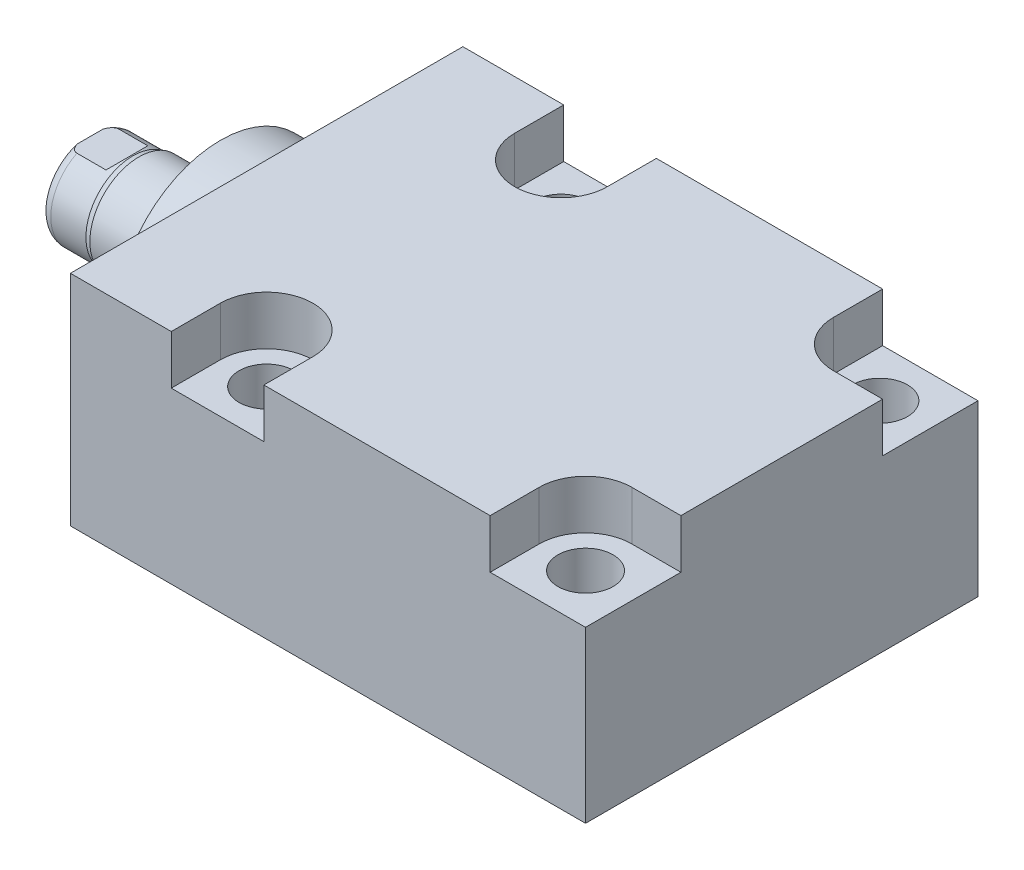
SolidWorks part; units mm, degrees
material "Alloy Steel"
ref_plane "Front Plane" through (0, 0, 0) normal (0, 0, 1) x (1, 0, 0)
ref_plane "Top Plane" through (0, 0, 0) normal (0, 1, 0) x (1, 0, 0)
ref_plane "Right Plane" through (0, 0, 0) normal (1, 0, 0) x (0, 0, -1)
ref_plane "Plane1" through (0, 0, 0) normal (1, 0, 0) x (0, 0, -1)
sketch "Sketch1" plane through (0, 0, 0) normal (1, 0, 0) x (0, 0, -1)
  line L0 (-25.4, 14.271) -> (25.4, 14.271)
  line L1 (25.4, 14.271) -> (25.4, -14.05)
  line L2 (25.4, -14.05) -> (-25.4, -14.05)
  line L3 (-25.4, -14.05) -> (-25.4, 14.271)
  line L4 (0, -24.4475) -> (0, 24.4475) construction
  dimension "D1" = 28.321
  dimension "D2" = 14.05
  dimension "D3" = 50.8
  dimension "D4" = 25.4
extrude "Extrude1" add sketch "Sketch1" along normal blind 66.675
sketch "Sketch5" plane through (0, 0, 0) normal (-1, 0, 0) x (0, 0, 1)
  circle A0 centre (0, 0) radius 13.5001
  dimension "D1" = 27.0002
extrude "Extrude2" add sketch "Sketch5" along normal blind 5.969
ref_plane "Plane5" through (0, 0, 0) normal (0, -1, 0) x (0, 0, 1)
sketch "Sketch6" plane through (0, 0, 0) normal (0, -1, 0) x (0, 0, 1)
  line L0 (0, 5.969) -> (-6.35, 5.969)
  line L1 (-6.35, 5.969) -> (-6.35, 22.86)
  line L2 (-6.35, 22.86) -> (0, 22.86)
  line L3 (0, 22.86) -> (0, 5.969)
  line L4 (0, -5.7546) -> (0, 21.1709) construction
  line L5 (13.5001, 5.969) -> (-13.5001, 5.969) construction
  line L6 (25.4, -66.675) -> (-25.4, -66.675) construction
  dimension "D1" = 89.535
  dimension "D2" = 12.7
revolve "Revolve1" add sketch "Sketch6" angle 360 about L4
ref_plane "Plane6" through (-18.5113, 3.2639, 0) normal (0, 0, 1) x (0, 1, 0)
sketch "S2D0001" plane through (-18.5113, 3.2639, 0) normal (0, 0, 1) x (0, 1, 0)
  line L0 (-0.7112, 2.7869) -> (-0.7112, -11.6533)
  line L1 (-3.2639, -13.1871) -> (-0.7112, -11.6533)
  line L2 (0.1905, 4.3487) -> (-3.2639, 4.3487)
  line L3 (-3.2639, 4.3487) -> (-3.2639, -13.1871)
  line L4 (-0.7112, 2.7869) -> (0.1905, 4.3487)
  line L5 (-3.2639, -18.5113) -> (-3.2639, 2.765) construction
  line L6 (3.0861, 4.3487) -> (-9.6139, 4.3487) construction
  dimension "D1" = 30
  dimension "D2" = 6.9088
  dimension "D3" = 5.1054
  dimension "D4" = 16.002
  dimension "D5" = 59
revolve "Cut-Revolve4" cut sketch "S2D0001" angle 360 about L5
ref_plane "Plane7" through (0, 0, 0) normal (0, 1, 0) x (0, 0, -1)
sketch "Sketch8" plane through (0, 0, 0) normal (0, 1, 0) x (0, 0, -1)
  line L0 (-6.35, 16.5354) -> (-6.096, 17.2974)
  line L1 (-6.096, 17.2974) -> (-6.096, 21.844)
  line L2 (0, 12.6594) -> (0, 20.8178) construction
  line L3 (-6.35, 16.5354) -> (-6.35, 22.86)
  line L4 (-5.7079, 22.86) -> (-6.35, 22.86)
  line L5 (6.35, 22.86) -> (-6.35, 22.86) construction
  line L6 (-6.35, 22.86) -> (-6.35, 5.969) construction
  arc A0 (-5.7079, 22.86) -> (-6.096, 21.844) centre (-4.572, 21.844) ccw
  dimension "D2" = 1.524
  dimension "D1" = 12.192
  dimension "D3" = 1.016
  dimension "D4" = 0.762
  dimension "D5" = 5.5626
revolve "Cut-Revolve5" cut sketch "Sketch8" angle 360 about L2
ref_plane "Plane11" through (0, 0, 0) normal (0, 0, -1) x (0, -1, 0)
sketch "Sketch12" plane through (0, 0, 0) normal (0, 0, -1) x (0, -1, 0)
  line L0 (5.461, 22.86) -> (5.461, 18.0848)
  line L1 (5.461, 18.0848) -> (6.096, 17.4498)
  line L2 (-5.461, 22.86) -> (-5.461, 18.0848)
  line L3 (-5.461, 18.0848) -> (-6.096, 17.4498)
  line L4 (5.461, 22.86) -> (6.096, 22.86)
  line L5 (0, 13.7262) -> (0, 20.767) construction
  line L6 (-6.096, 17.4498) -> (-6.096, 22.86)
  line L8 (6.096, 17.2974) -> (6.096, 21.844) construction
  line L9 (6.096, 17.4498) -> (6.096, 22.86)
  line L10 (-5.461, 22.86) -> (-6.096, 22.86)
  line L12 (5.7079, 22.86) -> (-5.7079, 22.86) construction
  dimension "D1" = 10.922
  dimension "D2" = 4.7752
  dimension "D3" = 45
extrude "Cut-Extrude4" cut sketch "Sketch12" against normal mid plane 60.96
hole_wizard "Hole2" positions "Sketch17" profile "Sketch16" legacy
sketch "Sketch17" plane through (0, 14.271, 0) normal (0, 1, 0) x (-1, 0, 0)
  line L0 (0, 0) -> (-59.3363, 0) construction
  line L1 (0, -25.4) -> (0, 25.4) construction
  point P0 (-19.05, -19.05)
  point P9 (-19.05, 19.05)
  dimension "D1" = 38.1
  dimension "D2" = 19.05
sketch "Sketch16" plane through (19.05, 14.271, -19.05) normal (1, 0, 0) x (0, 0, 1)
  line L0 (0, 0) -> (0, 28.321)
  line L1 (0, 28.321) -> (3.5687, 28.321)
  line L2 (3.5687, 28.321) -> (3.5687, 0)
  line L3 (3.5687, 0) -> (0, 0)
  line L4 (0, 110) -> (0, -10) construction
  dimension "Diameter" = 7.1374
  dimension "Depth" = 28.321
pattern_linear "LPattern1" count 2 spacing 41.275 along (1, 0, 0) of "Hole2"
sketch "Sketch18" plane through (0, 14.271, 0) normal (0, 1, 0) x (1, 0, 0)
  line L0 (0, 0) -> (50.053, 0) construction
  line L2 (66.675, -25.4) -> (0, -25.4) construction
  line L3 (66.675, 25.4) -> (66.675, -25.4) construction
  line L4 (66.675, -25.4) -> (54.3306, -25.4)
  line L5 (13.0556, -19.05) -> (13.0556, -25.4)
  line L6 (25.0444, -19.05) -> (25.0444, -25.4)
  line L7 (54.3306, -19.05) -> (54.3306, -25.4)
  line L8 (60.325, -13.0556) -> (66.675, -13.0556)
  line L9 (25.0444, -25.4) -> (13.0556, -25.4)
  line L10 (66.675, -13.0556) -> (66.675, -25.4)
  line L11 (66.675, 13.0556) -> (66.675, 25.4)
  line L12 (25.0444, 25.4) -> (13.0556, 25.4)
  line L13 (60.325, 13.0556) -> (66.675, 13.0556)
  line L14 (54.3306, 19.05) -> (54.3306, 25.4)
  line L15 (25.0444, 19.05) -> (25.0444, 25.4)
  line L16 (13.0556, 19.05) -> (13.0556, 25.4)
  line L17 (66.675, 25.4) -> (54.3306, 25.4)
  arc A0 (25.0444, -19.05) -> (13.0556, -19.05) centre (19.05, -19.05) ccw
  arc A1 (60.325, -13.0556) -> (54.3306, -19.05) centre (60.325, -19.05) ccw
  arc A2 (60.325, 13.0556) -> (54.3306, 19.05) centre (60.325, 19.05) cw
  arc A3 (25.0444, 19.05) -> (13.0556, 19.05) centre (19.05, 19.05) cw
  dimension "D1" = 11.9888
extrude "Cut-Extrude5" cut sketch "Sketch18" against normal blind 6.35
hole_wizard "Hole3" positions "Sketch20" profile "Sketch19" legacy
sketch "Sketch20" plane through (0, -14.05, 0) normal (0, -1, 0) x (1, 0, 0)
  line L0 (0, 25.4) -> (0, -25.4) construction
  point P0 (12.7, 0)
  dimension "D1" = 12.7
sketch "Sketch19" plane through (12.7, -14.05, 0) normal (1, 0, 0) x (0, 0, -1)
  line L0 (0, 0) -> (0, 14.9413)
  line L1 (0, 14.9413) -> (1.1938, 14.224)
  line L2 (1.1938, 14.224) -> (1.1938, 1.4478)
  line L3 (1.1938, 1.4478) -> (5.6705, 1.4478)
  line L4 (5.6705, 0) -> (0, 0)
  line L5 (0, -11.3109) -> (0, 121.1557) construction
  line L6 (0, 14.9413) -> (-1.1938, 14.224) construction
  line L7 (5.6705, 1.4478) -> (5.6705, 0)
  dimension "Depth" = 14.224
  dimension "Drill Angle" = 118
  dimension "Diameter" = 2.3876
  dimension "C-Bore Diameter" = 11.3411
  dimension "C-Bore Depth" = 1.4478
hole_wizard "Hole4" positions "Sketch21" profile "Sketch22" legacy
sketch "Sketch21" plane through (0, -14.05, 0) normal (0, -1, 0) x (1, 0, 0)
  point P0 (55.425, 0)
  dimension "D1" = 42.725
sketch "Sketch22" plane through (55.425, -14.05, 0) normal (1, 0, 0) x (0, 0, -1)
  line L0 (0, 0) -> (0, 15.1779)
  line L1 (0, 15.1779) -> (1.5875, 14.224)
  line L2 (1.5875, 14.224) -> (1.5875, 0)
  line L4 (1.5875, 0) -> (0, 0)
  line L5 (0, -11.3109) -> (0, 121.1557) construction
  line L6 (0, 15.1779) -> (-1.5875, 14.224) construction
  dimension "Depth" = 14.224
  dimension "Drill Angle" = 118
  dimension "Diameter" = 3.175
sketch "Sketch25" plane through (0, -14.05, 0) normal (0, -1, 0) x (1, 0, 0)
  circle A0 centre (53.975, 0) radius 5.6705
  dimension "D2" = 11.341
  dimension "D1" = 41.275
extrude "Cut-Extrude6" cut sketch "Sketch25" against normal blind 1.448
chamfer "Chamfer1" distance 0.635 angle 45 2 edges at (12.7, -12.6022, -1.1938) (55.425, -12.602, -1.5875)
sketch "Sketch23" plane through (0, 0, 0) normal (0, 0, 1) x (1, 0, 0)
  line L0 (12.7, -12.6022) -> (12.7, -21.4272) construction
  line L1 (10.8712, -12.6022) -> (14.5288, -12.6022) construction
  line L2 (7.0294, -12.6022) -> (18.3705, -12.6022) construction
  line L3 (7.0294, -12.6022) -> (7.0294, -14.05) construction
  circle A0 centre (8.4772, -14.05) radius 1.4478
  dimension "D1" = 2.8956
revolve "Revolve2" add sketch "Sketch23" angle 360 about L0
pattern_linear "LPattern3" count 2 spacing 41.275 along (1, 0, 0) of bodies 128
